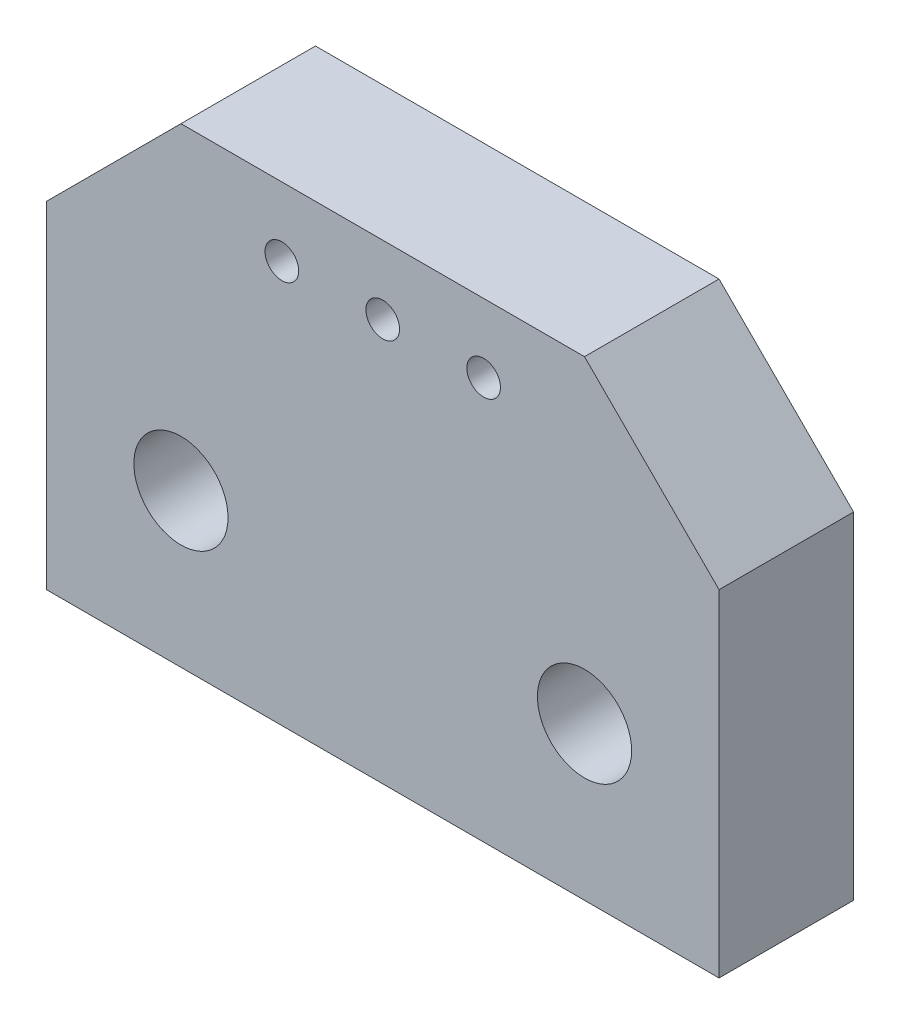
SolidWorks part; units mm, degrees
ref_plane "Front Plane" through (0, 0, 0) normal (0, 0, 1) x (1, 0, 0)
ref_plane "Top Plane" through (0, 0, 0) normal (0, 1, 0) x (1, 0, 0)
ref_plane "Right Plane" through (0, 0, 0) normal (1, 0, 0) x (0, 0, -1)
sketch "Sketch1" plane through (0, 0, 0) normal (0, 0, 1) x (1, 0, 0)
  line L0 (6.0971, 7) -> (6.0971, 0) construction
  line L1 (1.0971, 0) -> (1.0971, 5)
  line L2 (1.0971, 5) -> (3.0971, 7)
  line L3 (3.0971, 7) -> (9.0971, 7)
  line L4 (9.0971, 7) -> (11.0971, 5)
  line L5 (11.0971, 5) -> (11.0971, 0)
  line L6 (11.0971, 0) -> (1.0971, 0)
  dimension "D1" = 6
  dimension "D2" = 10
  dimension "D3" = 5
extrude "Boss-Extrude1" add sketch "Sketch1" along normal blind 2
hole_wizard "Ø1.4 (1.4) Diameter Hole1" positions "Sketch3" profile "Sketch2" hole size "Ø1.4" standard "ANSI Metric"
sketch "Sketch3" plane through (0, 0, 2) normal (0, 0, 1) x (1, 0, 0)
  line L0 (6.0971, 7) -> (6.0971, 0) construction
  line L1 (9.0971, 7) -> (3.0971, 7) construction
  line L2 (1.0971, 0) -> (11.0971, 0) construction
  point P0 (3.0971, 2.275)
  point P2 (9.0971, 2.275)
  dimension "D1" = 3
  dimension "D2" = 3
sketch "Sketch2" plane through (3.0971, 2.275, 2) normal (1, 0, 0) x (0, -1, 0)
  line L0 (0, 0) -> (0, 10.4206)
  line L1 (0, 10.4206) -> (0.7, 10)
  line L2 (0.7, 10) -> (0.7, 0)
  line L5 (0.7, 0) -> (0, 0)
  line L10 (0, 10.4206) -> (-0.7, 10) construction
  line L11 (0, -6.35) -> (0, 107.95) construction
  dimension "Hole Dia." = 1.4
  dimension "Hole Depth" = 10
  dimension "Drill Angle" = 118
hole_wizard "Ø0.5 (0.5) Diameter Hole1" positions "Sketch5" profile "Sketch4" hole size "Ø0.5" standard "ANSI Metric"
sketch "Sketch5" plane through (0, 0, 2) normal (0, 0, 1) x (1, 0, 0)
  line L0 (6.0971, 7) -> (6.0971, 0) construction
  line L1 (9.0971, 7) -> (3.0971, 7) construction
  line L2 (1.0971, 0) -> (11.0971, 0) construction
  point P0 (6.0971, 5.9793)
  point P2 (4.5971, 5.9793)
  point P4 (7.5971, 5.9793)
  dimension "D1" = 1.5
  dimension "D2" = 1.5
sketch "Sketch4" plane through (6.0971, 5.9793, 2) normal (1, 0, 0) x (0, -1, 0)
  line L0 (0, 0) -> (0, 10.1502)
  line L1 (0, 10.1502) -> (0.25, 10)
  line L2 (0.25, 10) -> (0.25, 0)
  line L5 (0.25, 0) -> (0, 0)
  line L10 (0, 10.1502) -> (-0.25, 10) construction
  line L11 (0, -6.35) -> (0, 107.95) construction
  dimension "Hole Dia." = 0.5
  dimension "Hole Depth" = 10
  dimension "Drill Angle" = 118
